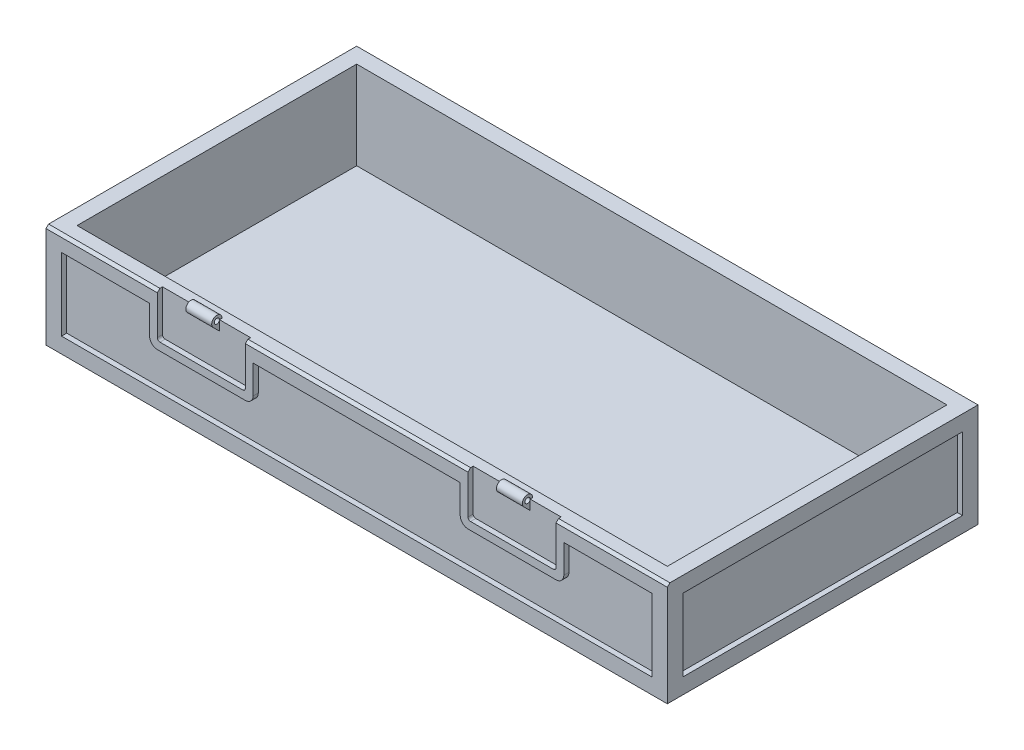
SolidWorks part; units mm, degrees
ref_plane "Front Plane" through (0, 0, 0) normal (0, 0, 1) x (1, 0, 0)
ref_plane "Top Plane" through (0, 0, 0) normal (0, 1, 0) x (1, 0, 0)
ref_plane "Right Plane" through (0, 0, 0) normal (1, 0, 0) x (0, 0, -1)
sketch "Sketch1" plane through (0, 0, 0) normal (0, 1, 0) x (1, 0, 0)
  line L1 (0, 0) -> (120, 0)
  line L2 (0, 0) -> (0, 60)
  line L3 (0, 60) -> (120, 60)
  line L4 (120, 0) -> (120, 60)
extrude "Boss-Extrude1" add sketch "Sketch1" along normal blind 20
sketch "Sketch2" plane through (0, 20, 0) normal (0, 1, 0) x (1, 0, 0)
  line L0 (0, 60) -> (3, 60)
  line L1 (120, 60) -> (0, 60) construction
  line L2 (3, 60) -> (3, 57)
  line L3 (3, 57) -> (117, 57)
  line L4 (117, 57) -> (117, 3)
  line L5 (117, 3) -> (3, 3)
  line L6 (3, 3) -> (3, 57)
extrude "Cut-Extrude1" cut sketch "Sketch2" against normal blind 17 contours L6 L5 L4 L3
sketch "Sketch3" plane through (0, 0, 0) normal (0, 0, 1) x (1, 0, 0)
  line L0 (0, 20) -> (21.5, 20)
  line L1 (0, 20) -> (120, 20) construction
  line L2 (21.5, 20) -> (21.5, 11.5)
  line L3 (21.5, 11.5) -> (38.5, 11.5)
  line L4 (38.5, 11.5) -> (38.5, 20)
  line L5 (21.5, 11.5) -> (22, 11.5)
  line L6 (22, 11.5) -> (22, 12)
  line L7 (38.5, 11.5) -> (38.5, 12)
  line L8 (38.5, 12) -> (38, 12)
  line L9 (21.5, 20) -> (38.5, 20)
  line L10 (60, 20) -> (60, 4.2953)
  line L11 (98.5, 20) -> (81.5, 20)
  line L12 (81.5, 12) -> (82, 12)
  line L13 (81.5, 11.5) -> (81.5, 12)
  line L14 (98, 11.5) -> (98, 12)
  line L15 (98.5, 11.5) -> (98, 11.5)
  line L16 (81.5, 11.5) -> (81.5, 20)
  line L17 (98.5, 11.5) -> (81.5, 11.5)
  line L18 (98.5, 20) -> (98.5, 11.5)
  circle A0 centre (22, 12) radius 0.5
  circle A1 centre (38, 12) radius 0.5
  circle A2 centre (82, 12) radius 0.5
  circle A3 centre (98, 12) radius 0.5
extrude "Cut-Extrude2" cut sketch "Sketch3" against normal blind 1
sketch "Sketch4" plane through (0, 0, 0) normal (0, 0, 1) x (1, 0, 0)
  line L0 (0, 20) -> (3, 20)
  line L1 (0, 20) -> (21.5, 20) construction
  line L2 (3, 20) -> (3, 3)
  line L3 (3, 3) -> (117, 3)
  line L4 (117, 3) -> (117, 17)
  line L5 (117, 17) -> (100, 17)
  line L6 (100, 17) -> (100, 10)
  line L7 (100, 10) -> (80, 10)
  line L8 (80, 10) -> (80, 17)
  line L9 (80, 17) -> (40, 17)
  line L10 (40, 17) -> (40, 10)
  line L11 (40, 10) -> (20, 10)
  line L12 (20, 10) -> (20, 17)
  line L13 (20, 17) -> (3, 17)
  line L14 (20, 10) -> (21.5, 10)
  line L15 (21.5, 10) -> (21.5, 11.5)
  line L16 (30, 10) -> (30, 11.8589)
  line L17 (60, 17) -> (60, 13.9656)
  line L18 (90, 10) -> (90, 11.8589)
  line L19 (98.5, 10) -> (98.5, 11.5)
  line L20 (100, 10) -> (98.5, 10)
  line L21 (80, 10) -> (100, 10)
  circle A0 centre (21.5, 11.5) radius 1.5
  circle A1 centre (38.5, 11.5) radius 1.5
  circle A2 centre (81.5, 11.5) radius 1.5
  circle A3 centre (98.5, 11.5) radius 1.5
extrude "Cut-Extrude3" cut sketch "Sketch4" against normal blind 1
sketch "Sketch5" plane through (0, 0, 0) normal (-1, 0, 0) x (0, 0, 1)
  line L0 (0, 20) -> (-3, 20)
  line L1 (-60, 20) -> (0, 20) construction
  line L2 (-3, 20) -> (-3, 0)
  line L3 (-60, 0) -> (0, 0) construction
  line L4 (-3, 0) -> (-3, 3)
  line L5 (-3, 3) -> (-60, 3)
  line L6 (-60, 20) -> (-60, 0) construction
  line L7 (-60, 3) -> (-57, 3)
  line L8 (-57, 3) -> (-57, 20)
  line L9 (-57, 20) -> (-57, 17)
  line L10 (-57, 17) -> (-3, 17)
extrude "Cut-Extrude4" cut sketch "Sketch5" against normal blind 1 contours L10 L8 L5 L2
sketch "Sketch6" plane through (120, 0, 0) normal (1, 0, 0) x (0, 0, -1)
  line L0 (0, 20) -> (3, 20)
  line L1 (0, 20) -> (60, 20) construction
  line L2 (3, 20) -> (3, 0)
  line L3 (0, 0) -> (60, 0) construction
  line L4 (3, 0) -> (3, 3)
  line L5 (3, 3) -> (60, 3)
  line L6 (60, 20) -> (60, 0) construction
  line L7 (60, 3) -> (57, 3)
  line L8 (57, 3) -> (57, 20)
  line L9 (57, 20) -> (57, 17)
  line L10 (57, 17) -> (3, 17)
extrude "Cut-Extrude5" cut sketch "Sketch6" against normal blind 1 contours L8 L10 L2 L5
sketch "Sketch7" plane through (0, 0, -60) normal (0, 0, -1) x (-1, 0, 0)
  line L0 (-120, 20) -> (-117, 20)
  line L1 (-120, 20) -> (0, 20) construction
  line L2 (-117, 20) -> (-117, 17)
  line L3 (-117, 17) -> (0, 17)
  line L4 (0, 20) -> (0, 0) construction
  line L5 (0, 17) -> (-3, 17)
  line L6 (-3, 17) -> (-3, 0)
  line L7 (-120, 0) -> (0, 0) construction
  line L8 (-3, 0) -> (-3, 3)
  line L9 (-3, 3) -> (-120, 3)
  line L10 (-120, 20) -> (-120, 0) construction
  line L11 (-120, 3) -> (-117, 3)
  line L12 (-117, 3) -> (-117, 17)
extrude "Cut-Extrude6" cut sketch "Sketch7" against normal blind 1 contours L12 L9 L6 L3
sketch "Sketch8" plane through (0, 0, 0) normal (0, -1, 0) x (1, 0, 0)
  line L0 (0, 0) -> (3, 0)
  line L1 (3, 0) -> (3, -60)
  line L2 (3, -60) -> (3, -57)
  line L3 (3, -57) -> (120, -57)
  line L4 (120, -57) -> (117, -57)
  line L5 (117, -57) -> (117, 0)
  line L6 (117, 0) -> (117, -3)
  line L7 (117, -3) -> (3, -3)
extrude "Cut-Extrude7" cut sketch "Sketch8" against normal blind 1 contours L5 L7 L1 L3
sketch "Sketch9" plane through (0, 0, -1) normal (0, 0, 1) x (1, 0, 0)
  line L0 (30, 20) -> (32.5, 20)
  line L1 (38.5, 20) -> (21.5, 20) construction
  line L2 (32.5, 20) -> (32.5, 21)
  line L3 (32.5, 21) -> (27.5, 21)
  line L4 (27.5, 21) -> (27.5, 18)
  line L5 (27.5, 18) -> (32.5, 18)
  line L6 (32.5, 20) -> (32.5, 18)
  line M9 (38.5, 20) -> (21.5, 20)
extrude "Boss-Extrude2" add sketch "Sketch9" along normal blind 3 and the other way blind 0.5 contours L6 L4 L5 M9 | L3 L4 L2 M9
sketch "Sketch11" plane through (32.5, 0, 0) normal (1, 0, 0) x (0, 0, -1)
  line L0 (1, 20) -> (0.5, 20)
  line L1 (0.5, 20) -> (-0.2071, 19.2929)
  line L2 (-0.2071, 19.2929) -> (1, 18.0858)
  line L3 (1, 20) -> (1, 18) construction
  line L5 (-2, 18) -> (1.5, 18)
  line L6 (-2, 18) -> (-2, 21)
  line L7 (-2, 21) -> (1.5, 21)
  line L8 (1.5, 18) -> (1.5, 21)
  circle A0 centre (0.5, 20) radius 0.5
  circle A1 centre (0.5, 20) radius 1
  line M3 (1, 18) -> (1, 20)
  line M5 (1.5, 20) -> (1.5, 21)
  line M6 (1.5, 21) -> (-2, 21)
  line M7 (-2, 21) -> (-2, 18)
  line M8 (-2, 18) -> (1, 18)
extrude "Cut-Extrude8" cut sketch "Sketch11" against normal blind 5 contours A1 L7 L2 M7 M8 M3 | A1 M5 M6 | L0 A0 L1 | L1 A0 L0
sketch "Sketch12" plane through (0, 0, -1) normal (0, 0, 1) x (1, 0, 0)
  line L0 (90, 20) -> (87.5, 20)
  line L1 (98.5, 20) -> (81.5, 20) construction
  line L2 (87.5, 20) -> (87.5, 21)
  line L3 (87.5, 21) -> (92.5, 21)
  line L4 (92.5, 21) -> (92.5, 18)
  line L5 (92.5, 18) -> (87.5, 18)
  line L6 (87.5, 18) -> (87.5, 20)
  line M4 (98.5, 20) -> (81.5, 20)
extrude "Boss-Extrude3" add sketch "Sketch12" along normal blind 2 and the other way blind 0.5 contours L6 L5 L4 M4
sketch "Sketch13" plane through (92.5, 0, 0) normal (1, 0, 0) x (0, 0, -1)
  line L0 (1, 20) -> (0.5, 20)
  line L1 (0.5, 20) -> (-0.2071, 19.2929)
  line L2 (-0.2071, 19.2929) -> (1, 18.0858)
  line L3 (1, 20) -> (1, 18) construction
  line L5 (-1, 18) -> (1.5, 18)
  line L6 (-1, 18) -> (-1, 21)
  line L7 (-1, 21) -> (1.5, 21)
  line L8 (1.5, 18) -> (1.5, 21)
  circle A0 centre (0.5, 20) radius 0.5
  circle A1 centre (0.5, 20) radius 1
  line M2 (1, 18) -> (1, 20)
  line M4 (1.5, 20) -> (1.5, 21)
  line M5 (1.5, 21) -> (-1, 21)
  line M6 (-1, 21) -> (-1, 18)
  line M7 (-1, 18) -> (1, 18)
extrude "Cut-Extrude9" cut sketch "Sketch13" against normal blind 5 contours A1 L7 L2 M6 M7 M2 | L1 A0 L0 | L0 A0 L1 | A1 M4 M5
sketch "Sketch14" plane through (0, 0, 0) normal (-1, 0, 0) x (0, 0, 1)
  line L0 (0, 20) -> (-0.5, 20)
  line L1 (-60, 20) -> (0, 20) construction
  line L2 (-0.5, 20) -> (-0.5, 19.5)
  line L3 (-0.5, 19.5) -> (0, 19.5)
  line L4 (0, 20) -> (0, 0) construction
  line L5 (0, 19.5) -> (-0.5, 20)
  line L6 (0, 20) -> (0, 19.5)
  line M7 (0, 0) -> (0, 20)
  line M8 (0, 20) -> (-60, 20)
extrude "Cut-Extrude10" cut sketch "Sketch14" against normal blind 23 contours L5 M7 M8
sketch "Sketch15" plane through (38.5, 0, 0) normal (-1, 0, 0) x (0, 0, 1)
  line L0 (0, 20) -> (-0.5, 20)
  line L1 (-1, 20) -> (0, 20) construction
  line L2 (0, 20) -> (0, 19.5)
  line L3 (0, 12) -> (0, 20) construction
  line L4 (0, 19.5) -> (-0.5, 20)
extrude "Cut-Extrude11" cut sketch "Sketch15" against normal blind 43
sketch "Sketch16" plane through (98.5, 0, 0) normal (-1, 0, 0) x (0, 0, 1)
  line L0 (0, 20) -> (-0.5, 20)
  line L1 (-1, 20) -> (0, 20) construction
  line L2 (0, 20) -> (0, 19.5)
  line L3 (0, 20) -> (0, 12) construction
  line L4 (0, 19.5) -> (-0.5, 20)
extrude "Cut-Extrude12" cut sketch "Sketch16" against normal blind 43
sketch "Sketch18" plane through (0, 0, 0) normal (0, -1, 0) x (-1, 0, 0)
  line L0 (0, 60) -> (-120, 0)
  line L1 (-60, 30) -> (-60, 24)
  line L2 (-60, 24) -> (-48, 24)
  line L3 (-48, 24) -> (-48, 36)
  line L4 (-48, 36) -> (-72, 36)
  line L5 (-72, 36) -> (-72, 24)
  line L6 (-72, 24) -> (-60, 24)
  line L7 (-60, 24) -> (-60, 22.5)
  line L8 (-60, 22.5) -> (-46.5, 22.5)
  line L9 (-46.5, 22.5) -> (-46.5, 37.5)
  line L10 (-46.5, 37.5) -> (-73.5, 37.5)
  line L11 (-73.5, 37.5) -> (-73.5, 22.5)
  line L12 (-73.5, 22.5) -> (-60, 22.5)
extrude "Boss-Extrude5" add sketch "Sketch18" against normal blind 1 contours L8 L9 L0 L3 L2 L7 | L11 L12 L7 L6 L0 | L10 L11 L0 L5 L4 L9
